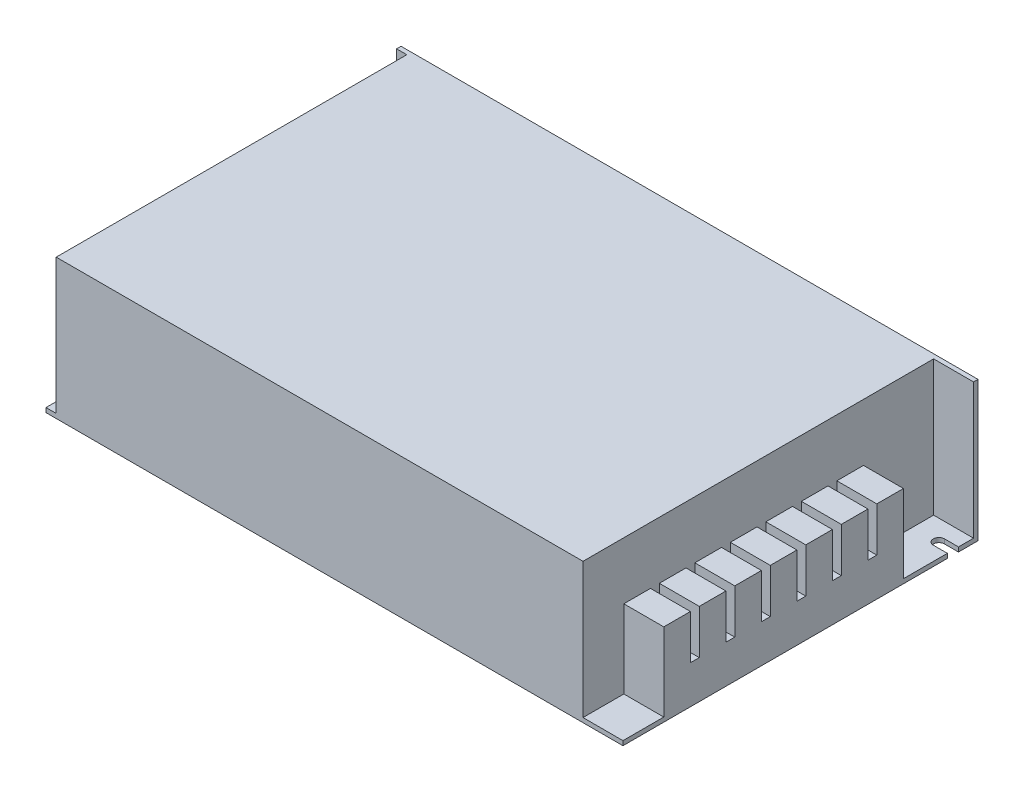
SolidWorks part; units mm, degrees
ref_plane "Front Plane" through (0, 0, 0) normal (0, 0, 1) x (1, 0, 0)
ref_plane "Top Plane" through (0, 0, 0) normal (0, 1, 0) x (1, 0, 0)
ref_plane "Right Plane" through (0, 0, 0) normal (1, 0, 0) x (0, 0, -1)
sketch "Sketch1" plane through (0, 0, 0) normal (0, 1, 0) x (1, 0, 0)
  line L1 (0, 0) -> (165.1, 0)
  line L2 (0, 0) -> (0, 101.6)
  line L3 (0, 101.6) -> (165.1, 101.6)
  line L4 (165.1, 0) -> (165.1, 101.6)
  dimension "D1" = 101.6
  dimension "D2" = 165.1
extrude "Boss-Extrude1" add sketch "Sketch1" along normal blind 40
sketch "Sketch2" plane through (165.1, 0, 0) normal (1, 0, 0) x (0, 0, -1)
  line L0 (0, 0) -> (101.6, 0) construction
  line L1 (0, 40) -> (100.33, 40)
  line L2 (0, 40) -> (0, 1.27)
  line L3 (0, 1.27) -> (100.33, 1.27)
  line L4 (100.33, 40) -> (100.33, 1.27)
  line L5 (0, 40) -> (100.33, 1.27) construction
  line L6 (0, 1.27) -> (100.33, 40) construction
  line L7 (101.6, 40) -> (101.6, 0) construction
  point P4 (50.165, 20.635)
  dimension "D1" = 1.27
  dimension "D2" = 1.27
extrude "Cut-Extrude1" cut sketch "Sketch2" against normal blind 11.43 contours L3 L4 L1 L2
sketch "Sketch3" plane through (0, 0, 0) normal (-1, 0, 0) x (0, 0, 1)
  line L4 (0, 1.27) -> (0, 40)
  line L5 (-100.33, 1.27) -> (0, 1.27)
  line L6 (-100.33, 40) -> (-100.33, 1.27)
  line L7 (0, 40) -> (-100.33, 40)
  line L8 (0, 1.27) -> (0, 40)
  line L9 (-100.33, 1.27) -> (0, 1.27)
  line L10 (-100.33, 40) -> (-100.33, 1.27)
  line L11 (0, 40) -> (-100.33, 40)
  dimension "D1" = 0
extrude "Cut-Extrude2" cut sketch "Sketch3" against normal blind 2.921
sketch "Sketch4" plane through (0, 1.27, 0) normal (0, 1, 0) x (1, 0, 0)
  line L0 (165.1, 0) -> (165.1, 100.33) construction
  line L1 (165.1, 11.684) -> (153.67, 11.684)
  line L2 (165.1, 11.684) -> (165.1, 80.264)
  line L3 (165.1, 80.264) -> (153.67, 80.264)
  line L4 (153.67, 11.684) -> (153.67, 80.264)
  line L5 (165.1, 11.684) -> (153.67, 80.264) construction
  line L6 (165.1, 80.264) -> (153.67, 11.684) construction
  line L7 (153.67, 0) -> (153.67, 100.33) construction
  line L8 (153.67, 0) -> (165.1, 0) construction
  point P4 (159.385, 45.974)
  dimension "D1" = 68.58
  dimension "D2" = 11.684
extrude "Boss-Extrude2" add sketch "Sketch4" along normal blind 22.352
sketch "Sketch5" plane through (0, 1.27, 0) normal (0, 1, 0) x (1, 0, 0)
  line L0 (0, 8.255) -> (0, 5.08)
  line L1 (0, 100.33) -> (0, 0) construction
  line L2 (0, 5.08) -> (4.0005, 5.08)
  line L3 (4.0005, 8.255) -> (0, 8.255)
  line L4 (165.1, 92.837) -> (165.1, 96.012)
  line L5 (165.1, 80.264) -> (165.1, 100.33) construction
  line L6 (165.1, 96.012) -> (161.0995, 96.012)
  line L7 (161.0995, 92.837) -> (165.1, 92.837)
  line L8 (165.1, 101.6) -> (0, 101.6) construction
  line L9 (2.921, 0) -> (0, 0) construction
  arc A0 (4.0005, 5.08) -> (4.0005, 8.255) centre (4.0005, 6.6675) ccw
  arc A1 (161.0995, 96.012) -> (161.0995, 92.837) centre (161.0995, 94.4245) ccw
  dimension "D2" = 5.588
  dimension "D1" = 3.175
  dimension "D3" = 5.588
  dimension "D4" = 5.08
extrude "Cut-Extrude3" cut sketch "Sketch5" against normal blind 22.352
sketch "Sketch6" plane through (0, 0, 0) normal (0, -1, 0) x (1, 0, 0)
  line L1 (165.1, 0) -> (165.1, -92.837) construction
  line L2 (0, 0) -> (165.1, 0) construction
  circle A0 centre (63.246, -65.278) radius 1.27
  circle A1 centre (140.97, -65.278) radius 1.27
  dimension "D1" = 80.264
  dimension "D2" = 64.008
  dimension "D3" = 22.86
  dimension "D4" = 2.54
extrude "Cut-Extrude4" cut sketch "Sketch6" against normal blind 10.16
sketch "Sketch7" plane through (0, 23.622, 0) normal (0, 1, 0) x (1, 0, 0)
  line L0 (153.67, 80.264) -> (153.67, 11.684) construction
  line L1 (165.1, 80.264) -> (153.67, 80.264)
  line L2 (165.1, 80.264) -> (165.1, 72.644)
  line L3 (165.1, 72.644) -> (153.67, 72.644)
  line L4 (153.67, 80.264) -> (153.67, 72.644)
  line L5 (159.385, 72.644) -> (159.385, 80.264) construction
  line L6 (165.1, 76.454) -> (153.67, 76.454) construction
  line L7 (159.385, 62.484) -> (159.385, 70.104) construction
  line L8 (165.1, 66.294) -> (153.67, 66.294) construction
  line L9 (165.1, 70.104) -> (165.1, 62.484)
  line L10 (165.1, 70.104) -> (153.67, 70.104)
  line L11 (153.67, 70.104) -> (153.67, 62.484)
  line L12 (165.1, 62.484) -> (153.67, 62.484)
  line L13 (159.385, 52.324) -> (159.385, 59.944) construction
  line L14 (165.1, 56.134) -> (153.67, 56.134) construction
  line L15 (165.1, 59.944) -> (165.1, 52.324)
  line L16 (165.1, 59.944) -> (153.67, 59.944)
  line L17 (153.67, 59.944) -> (153.67, 52.324)
  line L18 (165.1, 52.324) -> (153.67, 52.324)
  line L19 (159.385, 42.164) -> (159.385, 49.784) construction
  line L20 (165.1, 45.974) -> (153.67, 45.974) construction
  line L21 (165.1, 49.784) -> (165.1, 42.164)
  line L22 (165.1, 49.784) -> (153.67, 49.784)
  line L23 (153.67, 49.784) -> (153.67, 42.164)
  line L24 (165.1, 42.164) -> (153.67, 42.164)
  line L25 (159.385, 32.004) -> (159.385, 39.624) construction
  line L26 (165.1, 35.814) -> (153.67, 35.814) construction
  line L27 (165.1, 39.624) -> (165.1, 32.004)
  line L28 (165.1, 39.624) -> (153.67, 39.624)
  line L29 (153.67, 39.624) -> (153.67, 32.004)
  line L30 (165.1, 32.004) -> (153.67, 32.004)
  line L31 (159.385, 21.844) -> (159.385, 29.464) construction
  line L32 (165.1, 25.654) -> (153.67, 25.654) construction
  line L33 (165.1, 29.464) -> (165.1, 21.844)
  line L34 (165.1, 29.464) -> (153.67, 29.464)
  line L35 (153.67, 29.464) -> (153.67, 21.844)
  line L36 (165.1, 21.844) -> (153.67, 21.844)
  line L37 (159.385, 11.684) -> (159.385, 19.304) construction
  line L38 (165.1, 15.494) -> (153.67, 15.494) construction
  line L39 (165.1, 19.304) -> (165.1, 11.684)
  line L40 (165.1, 19.304) -> (153.67, 19.304)
  line L41 (153.67, 19.304) -> (153.67, 11.684)
  line L42 (165.1, 11.684) -> (153.67, 11.684)
  line L43 (159.385, 76.454) -> (159.385, 66.294) construction
  line L44 (165.1, 11.684) -> (165.1, 72.644)
  line L45 (153.67, 72.644) -> (153.67, 11.684)
  point P15 (159.385, 66.294)
  point P24 (159.385, 56.134)
  point P33 (159.385, 45.974)
  point P42 (159.385, 35.814)
  point P51 (159.385, 25.654)
  point P60 (159.385, 15.494)
  point P104 (159.385, 76.454)
  line M51 (165.1, 11.684) -> (165.1, 80.264)
  line M53 (153.67, 80.264) -> (153.67, 11.684)
  dimension "D2" = 10.16
  dimension "D3" = 7.62
  dimension "D1" = 7
extrude "Cut-Extrude5" cut sketch "Sketch7" against normal blind 12.7 contours L10 L3 M51 M53 | L16 L12 M51 M53 | L22 L18 M51 M53 | L28 L24 M51 M53 | L34 L30 M51 M53 | L40 L36 M51 M53
